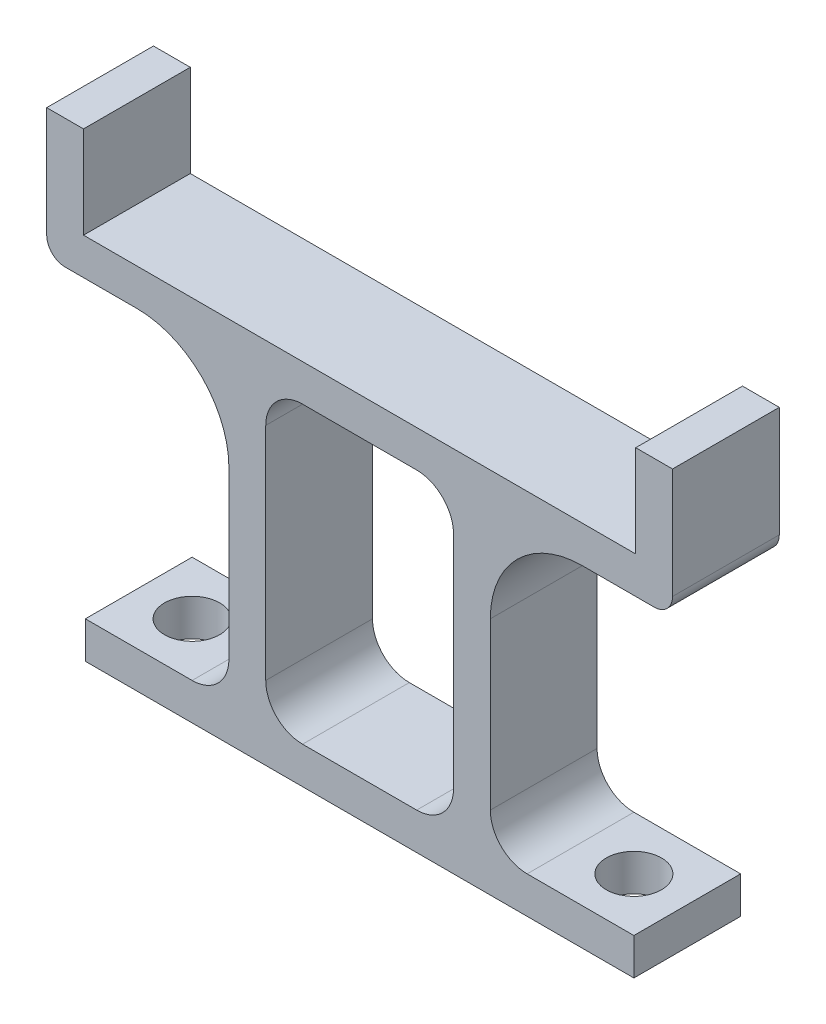
SolidWorks part; units mm, degrees
ref_plane "Front Plane" through (0, 0, 0) normal (0, 0, 1) x (1, 0, 0)
ref_plane "Top Plane" through (0, 0, 0) normal (0, 1, 0) x (1, 0, 0)
ref_plane "Right Plane" through (0, 0, 0) normal (1, 0, 0) x (0, 0, -1)
sketch "Sketch1" plane through (0, 0, 0) normal (0, 0, 1) x (1, 0, 0)
  line L0 (-15, 25) -> (-15, 20)
  line L1 (-15, 20) -> (15, 20)
  line L2 (15, 20) -> (15, 25)
  line L3 (15, 25) -> (17, 25)
  line L4 (17, 25) -> (17, 19)
  line L5 (16, 18) -> (12.1, 18)
  line L6 (-15, 25) -> (-17, 25)
  line L7 (-17, 25) -> (-17, 19)
  line L8 (-16, 18) -> (-12.1, 18)
  line L9 (-7.1, 13) -> (-7.1, 4)
  line L10 (-9.1, 2) -> (-14.9, 2)
  line L11 (-14.9, 2) -> (-14.9, 0)
  line L12 (-14.9, 0) -> (14.9, 0)
  line L13 (14.9, 0) -> (14.9, 2)
  line L14 (14.9, 2) -> (9.1, 2)
  line L15 (7.1, 4) -> (7.1, 13)
  line L16 (-7.1, 18) -> (7.1, 18) construction
  line L18 (-5.1, 18) -> (5.1, 18)
  line L19 (-5.1, 18) -> (-5.1, 2)
  line L20 (-5.1, 2) -> (5.1, 2)
  line L21 (5.1, 18) -> (5.1, 2)
  arc A0 (7.1, 13) -> (12.1, 18) centre (12.1, 13) cw
  arc A1 (-7.1, 13) -> (-12.1, 18) centre (-12.1, 13) ccw
  arc A2 (7.1, 4) -> (9.1, 2) centre (9.1, 4) ccw
  arc A3 (-7.1, 4) -> (-9.1, 2) centre (-9.1, 4) cw
  arc A4 (17, 19) -> (16, 18) centre (16, 19) cw
  arc A5 (-16, 18) -> (-17, 19) centre (-16, 19) cw
  point P8 (0, 20)
  point P17 (0, 18)
  point P19 (0, 0)
  point P30 (0, 0)
  point P31 (0, 0)
  point P36 (6.8532, 3)
  dimension "D11" = 5
  dimension "D12" = 2
  dimension "D14" = 1
  dimension "D1" = 30
  dimension "D2" = 2
  dimension "D3" = 2
  dimension "D4" = 5
  dimension "D5" = 2
  dimension "D6" = 18
  dimension "D7" = 2
  dimension "D8" = 2
  dimension "D9" = 2
  dimension "D10" = 29.8
  dimension "D13" = 5.8
extrude "Boss-Extrude1" add sketch "Sketch1" along normal blind 5.8
sketch "Sketch2" plane through (0, 2, 0) normal (0, 1, 0) x (1, 0, 0)
  line L0 (-14.9, -5.8) -> (-14.9, 0) construction
  line L1 (-9.1, 0) -> (-14.9, 0) construction
  line L2 (14.9, -5.8) -> (14.9, 0) construction
  line L3 (14.9, 0) -> (9.1, 0) construction
  circle A0 centre (-12, -2.9) radius 1.5
  circle A1 centre (12, -2.9) radius 1.5
  point P5 (-14.9, -2.9)
  point P8 (-12, 0)
  point P12 (14.9, -2.9)
  point P15 (12, 0)
  dimension "D1" = 3
extrude "Cut-Extrude1" cut sketch "Sketch2" against normal through all
fillet "Fillet1" radius 2 4 edges at (5.1, 2, 2.9) (-5.1, 2, 2.9) (5.1, 18, 2.9) (-5.1, 18, 2.9)
